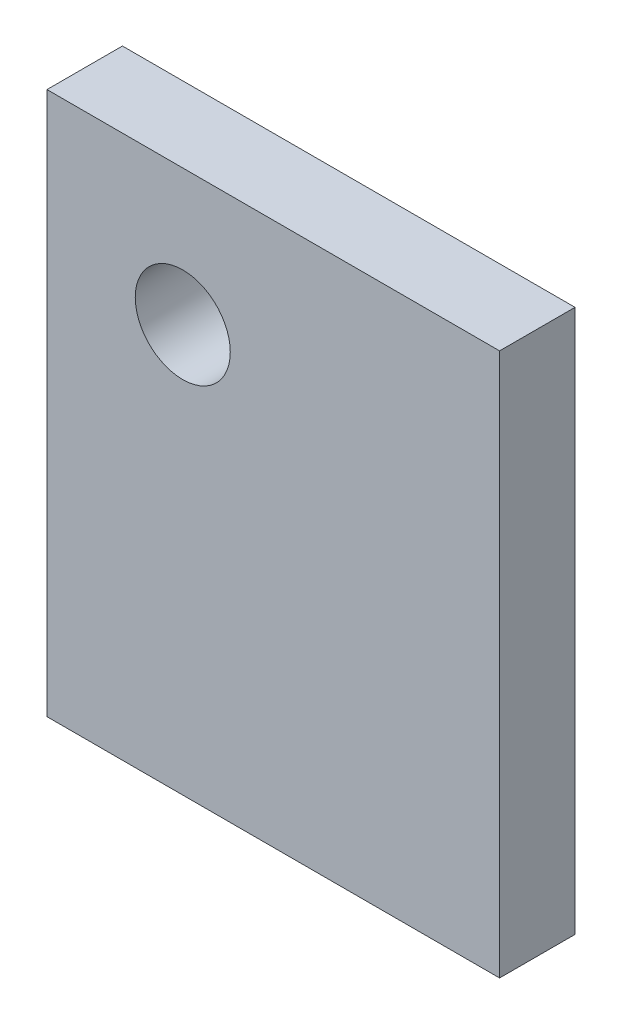
SolidWorks part; units mm, degrees
material "6061-T6 (SS)"
ref_plane "Front Plane" through (0, 0, 0) normal (0, 0, 1) x (1, 0, 0)
ref_plane "Top Plane" through (0, 0, 0) normal (0, 1, 0) x (1, 0, 0)
ref_plane "Right Plane" through (0, 0, 0) normal (1, 0, 0) x (0, 0, -1)
sketch "Sketch1" plane through (0, 0, 0) normal (0, 0, 1) x (1, 0, 0)
  line L1 (0, 0) -> (38.1, 0)
  line L2 (0, 0) -> (0, 45.72)
  line L3 (0, 45.72) -> (38.1, 45.72)
  line L4 (38.1, 0) -> (38.1, 45.72)
  dimension "D1" = 45.72
  dimension "D2" = 38.1
extrude "Boss-Extrude1" add sketch "Sketch1" along normal blind 6.35
sketch "Sketch2" plane through (0, 0, 6.35) normal (0, 0, 1) x (1, 0, 0)
  line L0 (38.1, 45.72) -> (0, 45.72) construction
  line L1 (0, 45.72) -> (0, 0) construction
  circle A0 centre (11.43, 34.29) radius 4
  dimension "D1" = 8
  dimension "D2" = 11.43
  dimension "D3" = 11.43
extrude "Cut-Extrude1" cut sketch "Sketch2" against normal through all both and the other way through all
